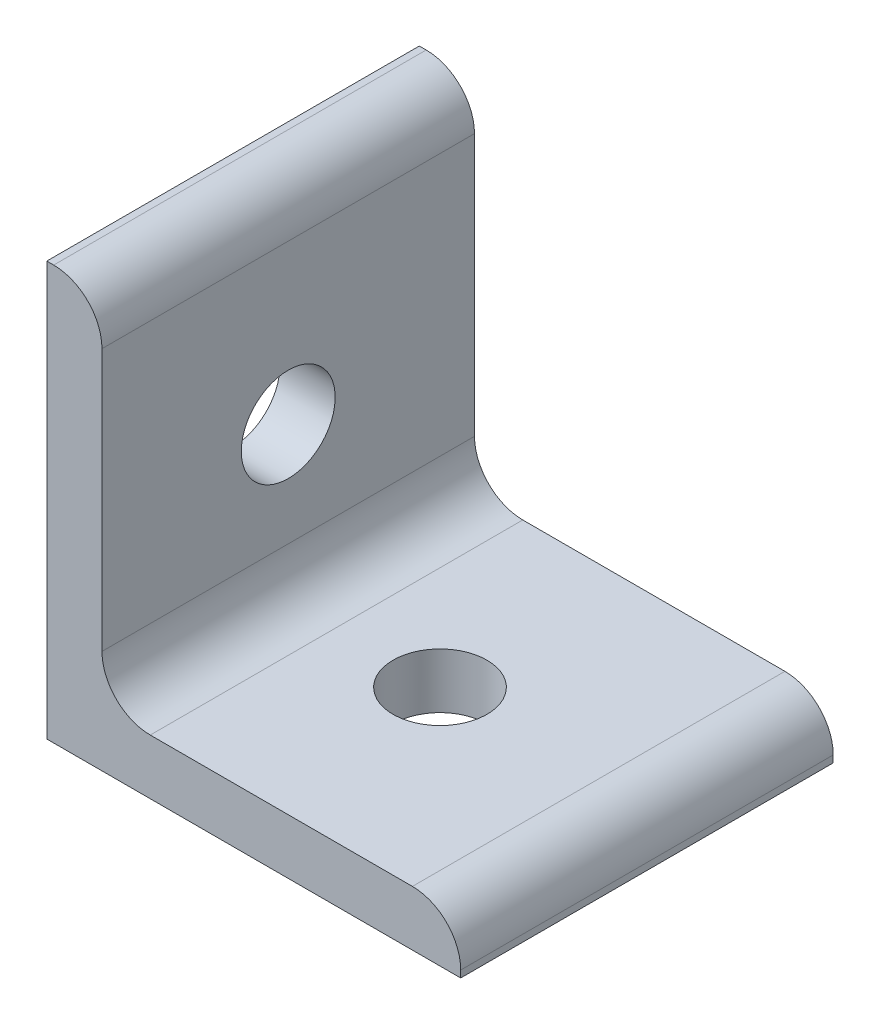
SolidWorks part; units mm, degrees
material "6105-T5 Aluminum"
ref_plane "Front Plane" through (0, 0, 0) normal (0, 0, 1) x (1, 0, 0)
ref_plane "Top Plane" through (0, 0, 0) normal (0, 1, 0) x (1, 0, 0)
ref_plane "Right Plane" through (0, 0, 0) normal (1, 0, 0) x (0, 0, -1)
sketch "Sketch1" plane through (0, 0, 0) normal (0, 0, 1) x (1, 0, 0)
  line L1 (0, 0) -> (30, 0)
  line L2 (0, 0) -> (0, 30)
  line L3 (0, 30) -> (0.5, 30)
  line L4 (30, 0) -> (30, 0.5)
  line L7 (26.5, 4) -> (7.5, 4)
  line L8 (4, 26.5) -> (4, 7.5)
  arc A0 (30, 0.5) -> (26.5, 4) centre (26.5, 0.5) ccw
  arc A1 (0.5, 30) -> (4, 26.5) centre (0.5, 26.5) cw
  arc A2 (7.5, 4) -> (4, 7.5) centre (7.5, 7.5) cw
  dimension "D5" = 3.5
  dimension "D6" = 3.5
  dimension "D1" = 4
  dimension "D2" = 4
  dimension "D3" = 30
  dimension "D4" = 30
extrude "Boss-Extrude1" add sketch "Sketch1" against normal mid plane 27
sketch "Sketch4" plane through (0, 0, 0) normal (-1, 0, 0) x (0, 0, 1)
  line L0 (0, 0) -> (0, 15) construction
  circle A0 centre (0, 15) radius 3.4036
  dimension "D1" = 6.8072
  dimension "D2" = 15
extrude "Cut-Extrude3" cut sketch "Sketch4" against normal blind 10
sketch "Sketch5" plane through (0, 0, 0) normal (0, -1, 0) x (1, 0, 0)
  line L0 (0, 0) -> (15, 0) construction
  circle A0 centre (15, 0) radius 3.4036
  dimension "D1" = 6.8072
  dimension "D2" = 15
extrude "Cut-Extrude4" cut sketch "Sketch5" against normal blind 10
